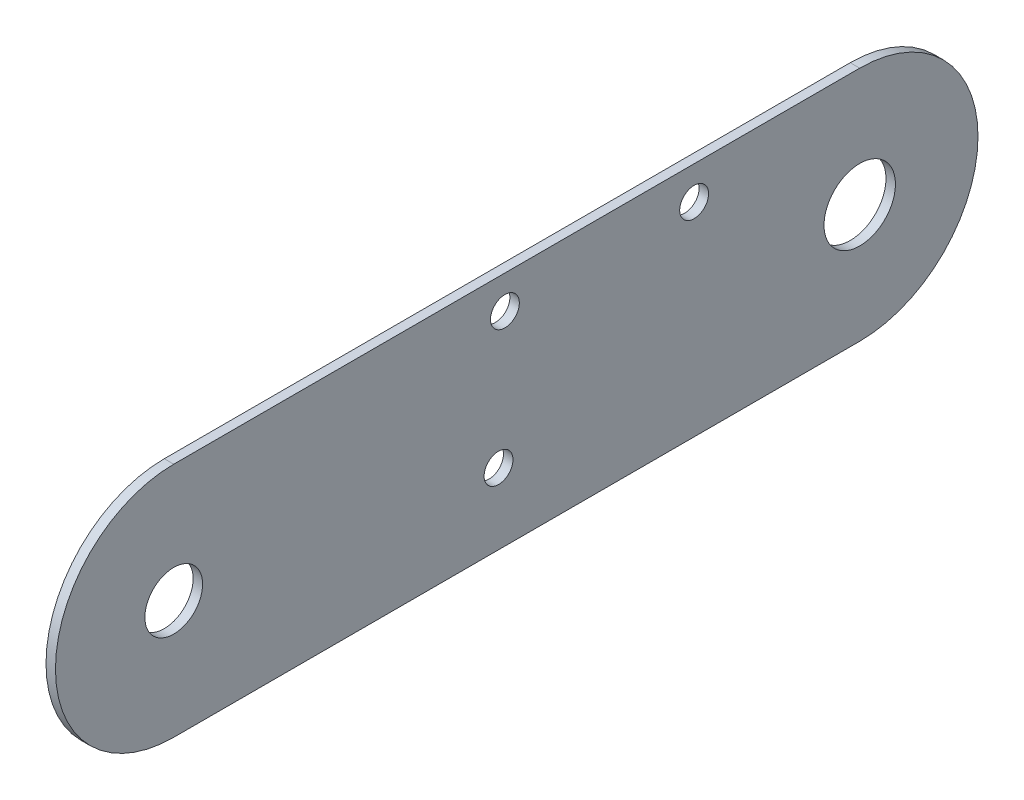
SolidWorks part; units mm, degrees
ref_plane "前视基准面" through (0, 0, 0) normal (0, 0, 1) x (1, 0, 0)
ref_plane "上视基准面" through (0, 0, 0) normal (0, 1, 0) x (1, 0, 0)
ref_plane "右视基准面" through (0, 0, 0) normal (1, 0, 0) x (0, 0, -1)
sketch "草图1" plane through (0, 0, 0) normal (1, 0, 0) x (0, 0, -1)
  line L0 (91.077, 40.4552) -> (33.8601, -58.6474) construction
  line L1 (19.4263, -58.6474) -> (-125.5737, -58.6474)
  line L2 (-134.9038, -36.1474) -> (137.7276, 121.2564) construction
  line L3 (23.3434, -40.432) -> (64.5291, -111.7676) construction
  line L4 (-240.8626, -64.5389) -> (49.2974, 13.2092) construction
  line L5 (140.7147, 124.2435) -> (-66.5738, -83.0449) construction
  line L6 (153.5693, 198.695) -> (-51.0405, -155.6994) construction
  line L7 (194.3644, -33.6474) -> (-306.5717, -33.6474) construction
  line L8 (69.4263, 52.9552) -> (-125.5737, -33.6474) construction
  line L9 (4.9926, -8.6474) -> (-125.5737, -8.6474)
  line L10 (47.7757, 65.4552) -> (4.9926, -8.6474) construction
  line L11 (137.7276, 121.2564) -> (91.077, 40.4552) construction
  line L12 (4.9926, -8.6474) -> (19.4263, -8.6474)
  line L13 (-184.3419, -15.6474) -> (79.5959, -15.6474) construction
  line L14 (-125.5737, -33.6474) -> (-125.5737, 86.0203) construction
  circle A0 centre (19.4263, -33.6474) radius 7.55
  circle A1 centre (-125.5737, -33.6474) radius 6.1
  circle A2 centre (69.4263, 52.9552) radius 3.25 construction
  arc A3 (91.077, 40.4552) -> (47.7757, 65.4552) centre (69.4263, 52.9552) ccw construction
  arc A4 (-125.5737, -8.6474) -> (-125.5737, -58.6474) centre (-125.5737, -33.6474) ccw
  circle A5 centre (-56.9216, -43.6474) radius 3.05
  arc A8 (19.4263, -58.6474) -> (19.4263, -8.6474) centre (19.4263, -33.6474) ccw
  circle A9 centre (-15.5737, -15.6474) radius 3.05
  circle A10 centre (-55.5737, -15.6474) radius 3.05
  point P10 (0, 0)
  point P17 (-125.5737, -33.6474)
  point P18 (69.4263, 52.9552)
  dimension "D6" = 15.1
  dimension "D8" = 12.2
  dimension "D10" = 6.5
  dimension "D13" = 6.1
  dimension "D14" = 77
  dimension "D15" = 15
  dimension "D16" = 50
  dimension "D18" = 6.1
  dimension "D19" = 40
  dimension "D20" = 70
  dimension "D2" = 120
  dimension "D3" = 30
  dimension "D4" = 15
  dimension "D5" = 15
  dimension "D7" = 207.735
  dimension "D9" = 100
  dimension "D11" = 50
  dimension "D12" = 145
  dimension "D17" = 18
extrude "凸台-拉伸1" add sketch "草图1" along normal blind 2
